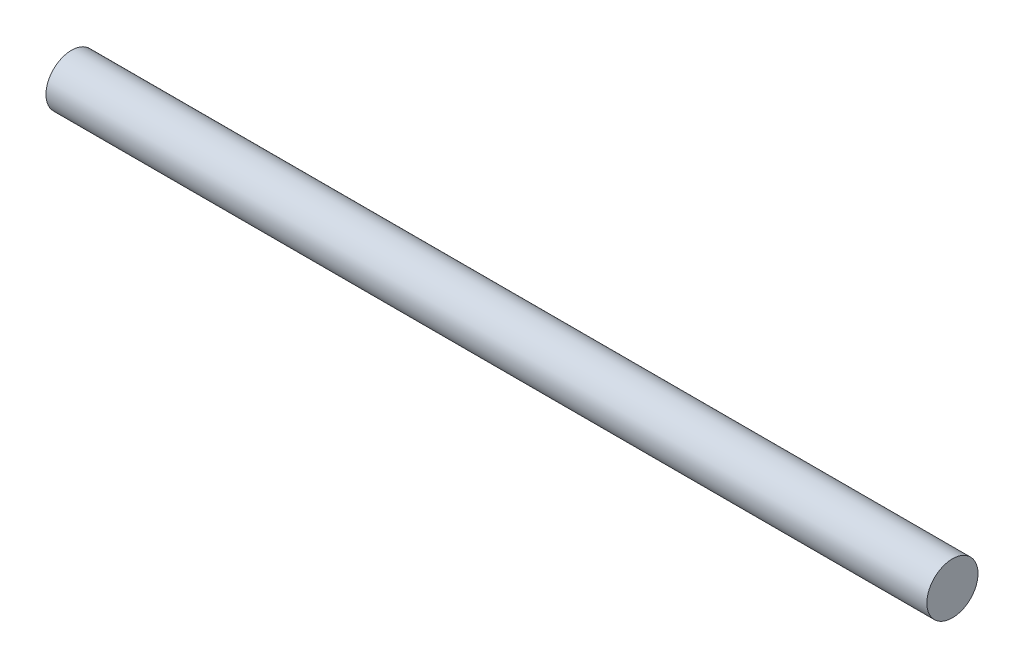
SolidWorks part; units mm, degrees
ref_plane "Plan de face" through (0, 0, 0) normal (0, 0, 1) x (1, 0, 0)
ref_plane "Plan de dessus" through (0, 0, 0) normal (0, 1, 0) x (1, 0, 0)
ref_plane "Plan de droite" through (0, 0, 0) normal (1, 0, 0) x (0, 0, -1)
sketch "Esquisse5" plane through (0, 0, 0) normal (1, 0, 0) x (0, 0, -1)
  circle A0 centre (0, 0) radius 18
extrude "Boss.-Extru.3" add sketch "Esquisse5" along normal blind 620
ref_plane "Plan2" through (10, 0, 0) normal (-1, 0, 0) x (0, 0, 1)
ref_plane "Plan4" through (610, 0, 0) normal (-1, 0, 0) x (0, 0, 1)
sketch "Esquisse6" plane through (10, 0, 0) normal (-1, 0, 0) x (0, 0, 1)
  circle A0 centre (0, 0) radius 18
sketch "Esquisse7" plane through (610, 0, 0) normal (-1, 0, 0) x (0, 0, 1)
  circle A0 centre (0, 0) radius 18
ref_plane "Plan8" through (70, 0, 0) normal (-1, 0, 0) x (0, 0, 1)
ref_plane "Plan9" through (96, 0, 0) normal (-1, 0, 0) x (0, 0, 1)
sketch "Esquisse12" plane through (70, 0, 0) normal (-1, 0, 0) x (0, 0, 1)
  circle A0 centre (0, 0) radius 18
sketch "Esquisse13" plane through (96, 0, 0) normal (-1, 0, 0) x (0, 0, 1)
  circle A0 centre (0, 0) radius 18
ref_plane "Plan15" through (122, 0, 0) normal (-1, 0, 0) x (0, 0, 1)
ref_plane "Plan16" through (148, 0, 0) normal (-1, 0, 0) x (0, 0, 1)
sketch "Esquisse18" plane through (122, 0, 0) normal (-1, 0, 0) x (0, 0, 1)
  circle A0 centre (0, 0) radius 18
sketch "Esquisse19" plane through (148, 0, 0) normal (-1, 0, 0) x (0, 0, 1)
  circle A0 centre (0, 0) radius 18
ref_plane "Plan18" through (174, 0, 0) normal (-1, 0, 0) x (0, 0, 1)
ref_plane "Plan19" through (264, 0, 0) normal (-1, 0, 0) x (0, 0, 1)
ref_plane "Plan20" through (284, 0, 0) normal (-1, 0, 0) x (0, 0, 1)
ref_plane "Plan21" through (324, 0, 0) normal (-1, 0, 0) x (0, 0, 1)
ref_plane "Plan22" through (344, 0, 0) normal (-1, 0, 0) x (0, 0, 1)
ref_plane "Plan23" through (418, 0, 0) normal (-1, 0, 0) x (0, 0, 1)
sketch "Esquisse20" plane through (174, 0, 0) normal (-1, 0, 0) x (0, 0, 1)
  circle A0 centre (0, 0) radius 18
sketch "Esquisse21" plane through (264, 0, 0) normal (-1, 0, 0) x (0, 0, 1)
  circle A0 centre (0, 0) radius 18
sketch "Esquisse22" plane through (284, 0, 0) normal (-1, 0, 0) x (0, 0, 1)
  circle A0 centre (0, 0) radius 18
sketch "Esquisse23" plane through (324, 0, 0) normal (-1, 0, 0) x (0, 0, 1)
  circle A0 centre (0, 0) radius 18
sketch "Esquisse24" plane through (344, 0, 0) normal (-1, 0, 0) x (0, 0, 1)
  circle A0 centre (0, 0) radius 18
sketch "Esquisse25" plane through (418, 0, 0) normal (-1, 0, 0) x (0, 0, 1)
  circle A0 centre (0, 0) radius 18
ref_plane "Plan25" through (444, 0, 0) normal (-1, 0, 0) x (0, 0, 1)
ref_plane "Plan26" through (470, 0, 0) normal (-1, 0, 0) x (0, 0, 1)
ref_plane "Plan27" through (496, 0, 0) normal (-1, 0, 0) x (0, 0, 1)
ref_plane "Plan28" through (522, 0, 0) normal (-1, 0, 0) x (0, 0, 1)
ref_plane "Plan29" through (548, 0, 0) normal (-1, 0, 0) x (0, 0, 1)
sketch "Esquisse26" plane through (444, 0, 0) normal (-1, 0, 0) x (0, 0, 1)
  circle A0 centre (0, 0) radius 18
sketch "Esquisse27" plane through (470, 0, 0) normal (-1, 0, 0) x (0, 0, 1)
  circle A0 centre (0, 0) radius 18
sketch "Esquisse28" plane through (496, 0, 0) normal (-1, 0, 0) x (0, 0, 1)
  circle A0 centre (0, 0) radius 18
sketch "Esquisse29" plane through (522, 0, 0) normal (-1, 0, 0) x (0, 0, 1)
  circle A0 centre (0, 0) radius 18
sketch "Esquisse30" plane through (548, 0, 0) normal (-1, 0, 0) x (0, 0, 1)
  circle A0 centre (0, 0) radius 18
ref_plane "Plan30" through (200, 0, 0) normal (-1, 0, 0) x (0, 0, 1)
sketch "Esquisse31" plane through (200, 0, 0) normal (-1, 0, 0) x (0, 0, 1)
  circle A0 centre (0, 0) radius 18
